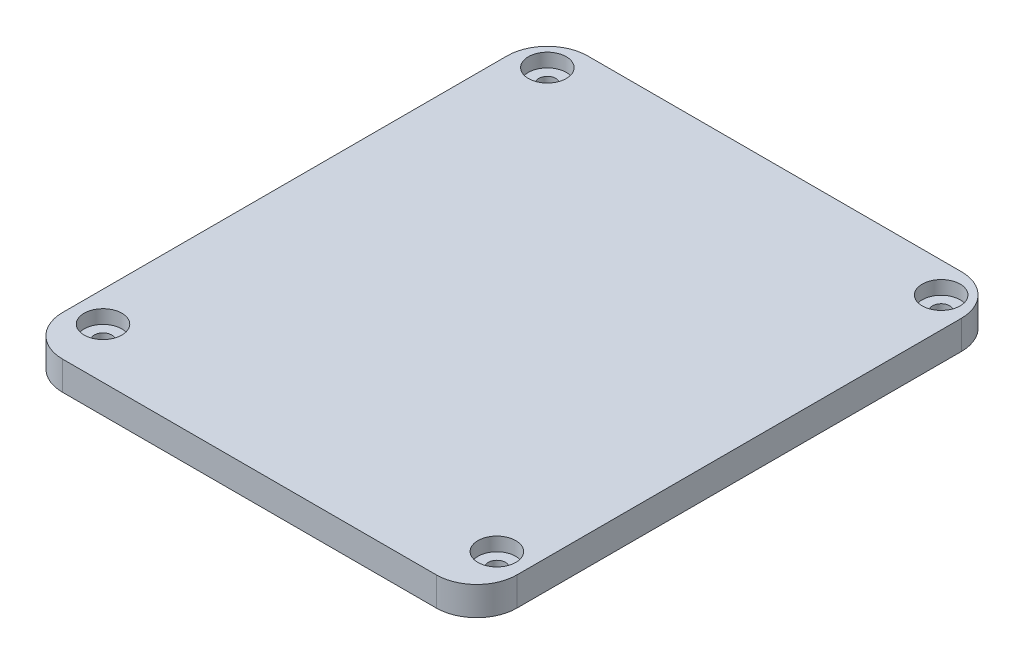
SolidWorks part; units mm, degrees
ref_plane "Спереди" through (0, 0, 0) normal (0, 0, 1) x (1, 0, 0)
ref_plane "Сверху" through (0, 0, 0) normal (0, 1, 0) x (1, 0, 0)
ref_plane "Справа" through (0, 0, 0) normal (1, 0, 0) x (0, 0, -1)
sketch "Sketch1" plane through (0, 0, 0) normal (0, 1, 0) x (1, 0, 0)
  line L1 (45, -50) -> (-45, -50)
  line L2 (45, -50) -> (45, 50)
  line L3 (45, 50) -> (-45, 50)
  line L4 (-45, -50) -> (-45, 50)
  line L5 (45, -50) -> (-45, 50) construction
  line L6 (45, 50) -> (-45, -50) construction
  point P0 (0, 0)
  dimension "D1" = 90
  dimension "D2" = 100
extrude "Boss-Extrude1" add sketch "Sketch1" along normal blind 3
sketch "Sketch2" plane through (0, 3, 0) normal (0, 1, 0) x (1, 0, 0)
  line L0 (-45, 50) -> (-45, -50) construction
  line L1 (39, -44) -> (-39, -44) construction
  line L2 (39, -44) -> (39, 44) construction
  line L3 (39, 44) -> (-39, 44) construction
  line L4 (-39, -44) -> (-39, 44) construction
  line L5 (39, -44) -> (-39, 44) construction
  line L6 (39, 44) -> (-39, -44) construction
  line L7 (45, 50) -> (-45, 50) construction
  circle A0 centre (-39, 44) radius 1.7
  circle A1 centre (39, 44) radius 1.7
  circle A2 centre (39, -44) radius 1.7
  circle A3 centre (-39, -44) radius 1.7
  point P0 (0, 0)
  dimension "D3" = 3.4
  dimension "D1" = 6
  dimension "D2" = 6
extrude "Cut-Extrude1" cut sketch "Sketch2" against normal through all
sketch "Sketch4" plane through (0, 0, 0) normal (0, -1, 0) x (1, 0, 0)
  line L0 (-45, -50) -> (-45, 50) construction
  line L1 (41.6, 46.6) -> (-38.6, 46.6)
  line L2 (41.6, 46.6) -> (41.6, -46.6)
  line L3 (41.6, -46.6) -> (-38.6, -46.6)
  line L4 (-38.6, 46.6) -> (-38.6, -46.6)
  line L5 (-45, 50) -> (45, 50) construction
  line L6 (45, 50) -> (45, -50) construction
  line L7 (45, -50) -> (-45, -50) construction
  line L9 (38.6, 43.6) -> (-35.6, 43.6)
  line L10 (38.6, 43.6) -> (38.6, -43.6)
  line L11 (38.6, -43.6) -> (-35.6, -43.6)
  line L12 (-35.6, 43.6) -> (-35.6, -43.6)
  point P0 (0, 0)
  point P10 (0, 0)
  dimension "D1" = 6.4
  dimension "D2" = 3.4
  dimension "D3" = 3
  dimension "D4" = 3
  dimension "D5" = 3
  dimension "D6" = 3.4
  dimension "D7" = 3
  dimension "D8" = 3.4
extrude "Boss-Extrude2" add sketch "Sketch4" along normal blind 2
sketch "Sketch6" plane through (0, 3, 0) normal (0, 1, 0) x (1, 0, 0)
  line L0 (45, -50) -> (45, 50) construction
  circle A0 centre (-39, 44) radius 6
  circle A1 centre (-39, -44) radius 6
  circle A2 centre (39, -44) radius 6
  circle A3 centre (39, 44) radius 6
extrude "Cut-Extrude5" cut sketch "Sketch6" against normal through all from offset 3 offset against normal yes
sketch "Sketch7" plane through (0, 0, 50) normal (0, 0, 1) x (1, 0, 0)
  line L0 (-45, 3) -> (-45, 0)
  line L1 (-45, 0) -> (45, 0)
  line L2 (45, 0) -> (45, 3)
  line L3 (45, 3) -> (-45, 3)
extrude "Boss-Extrude3" add sketch "Sketch7" along normal blind 4
sketch "Sketch8" plane through (0, 3, 0) normal (0, 1, 0) x (1, 0, 0)
  line L0 (-45, -50) -> (-45, -54)
  line L1 (-45, -54) -> (45, -54)
  line L2 (45, -50) -> (45, 50)
  line L3 (45, 50) -> (-45, 50)
  line L4 (-45, -50) -> (-45, 50)
  line L5 (45, -50) -> (-45, 50) construction
  line L6 (45, 50) -> (-45, -50) construction
  line L7 (45, -54) -> (45, -50)
  circle A1 centre (-39, 44) radius 3.75
  circle A3 centre (39, 44) radius 3.75
  circle A6 centre (-39, -44) radius 3.75
  circle A7 centre (39, -44) radius 3.75
  point P0 (0, 0)
  dimension "D1" = 7.5
extrude "Boss-Extrude4" add sketch "Sketch8" along normal blind 2.7
fillet "Fillet1" radius 8 4 edges at (-45, 2.85, -50) (-45, 2.85, 54) (45, 2.85, -50) (45, 2.85, 54)
